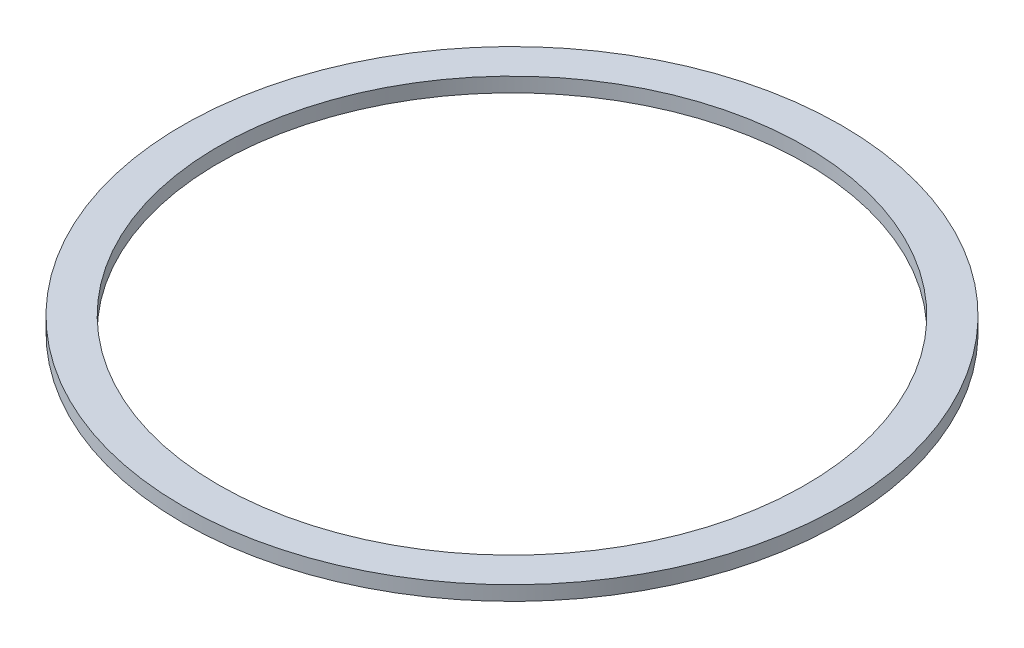
SolidWorks part; units mm, degrees
ref_plane "Front Plane" through (0, 0, 0) normal (0, 0, 1) x (1, 0, 0)
ref_plane "Top Plane" through (0, 0, 0) normal (0, 1, 0) x (1, 0, 0)
ref_plane "Right Plane" through (0, 0, 0) normal (1, 0, 0) x (0, 0, -1)
sketch "Sketch1" plane through (0, 0, 0) normal (0, 1, 0) x (1, 0, 0)
  circle A0 centre (0, 0) radius 28.8925
  circle A1 centre (0, 0) radius 25.7175
  dimension "D1" = 57.785
  dimension "D2" = 51.435
extrude "Boss-Extrude1" add sketch "Sketch1" along normal blind 1.27
